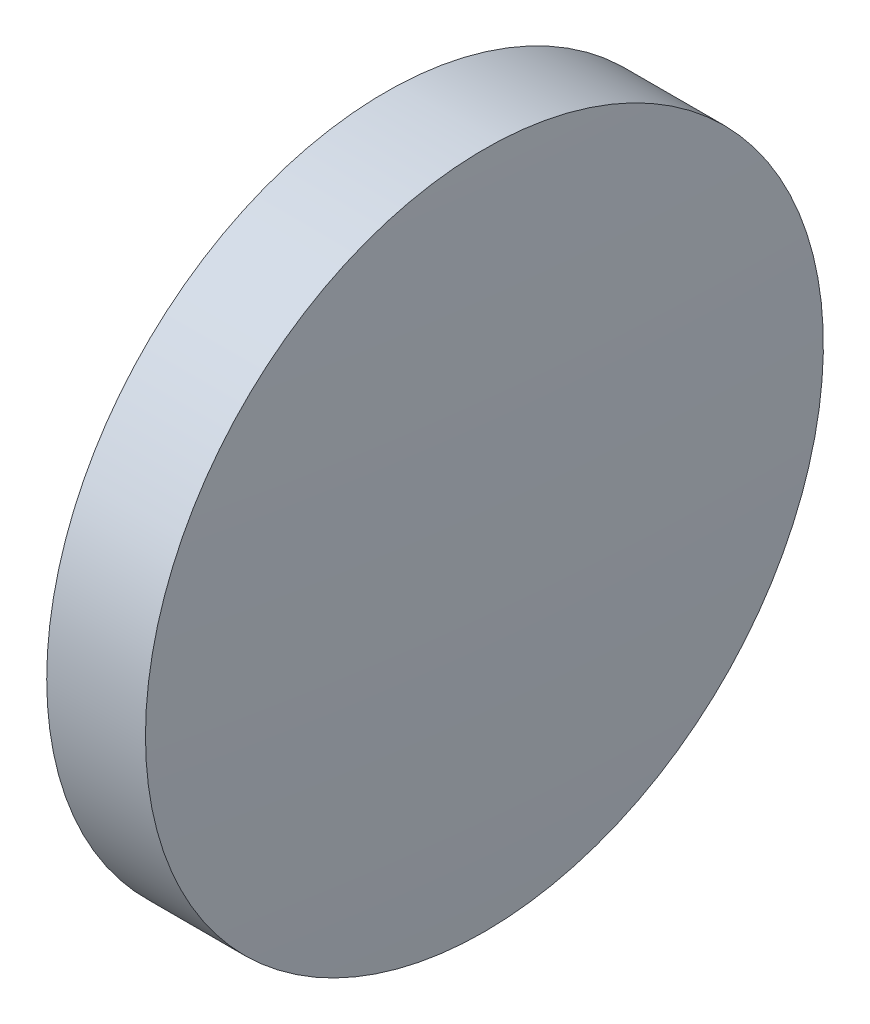
SolidWorks part; units mm, degrees
ref_plane "前视基准面" through (0, 0, 0) normal (0, 0, 1) x (1, 0, 0)
ref_plane "上视基准面" through (0, 0, 0) normal (0, 1, 0) x (1, 0, 0)
ref_plane "右视基准面" through (0, 0, 0) normal (1, 0, 0) x (0, 0, -1)
sketch "草图1" plane through (0, 0, 0) normal (0, 0, 1) x (1, 0, 0)
  line L0 (420.8796, 74.7634) -> (439.6756, 74.7634) construction
  line L1 (426.6179, 74.7634) -> (426.6179, 87.4634)
  line L2 (430.6179, 74.7634) -> (426.6179, 74.7634)
  line L5 (426.6179, 87.4634) -> (430.3179, 87.4634)
  arc A0 (430.6179, 74.7634) -> (430.3179, 87.4634) centre (161.6512, 74.7634) ccw
revolve "旋转1" add sketch "草图1" angle 360 about L0
